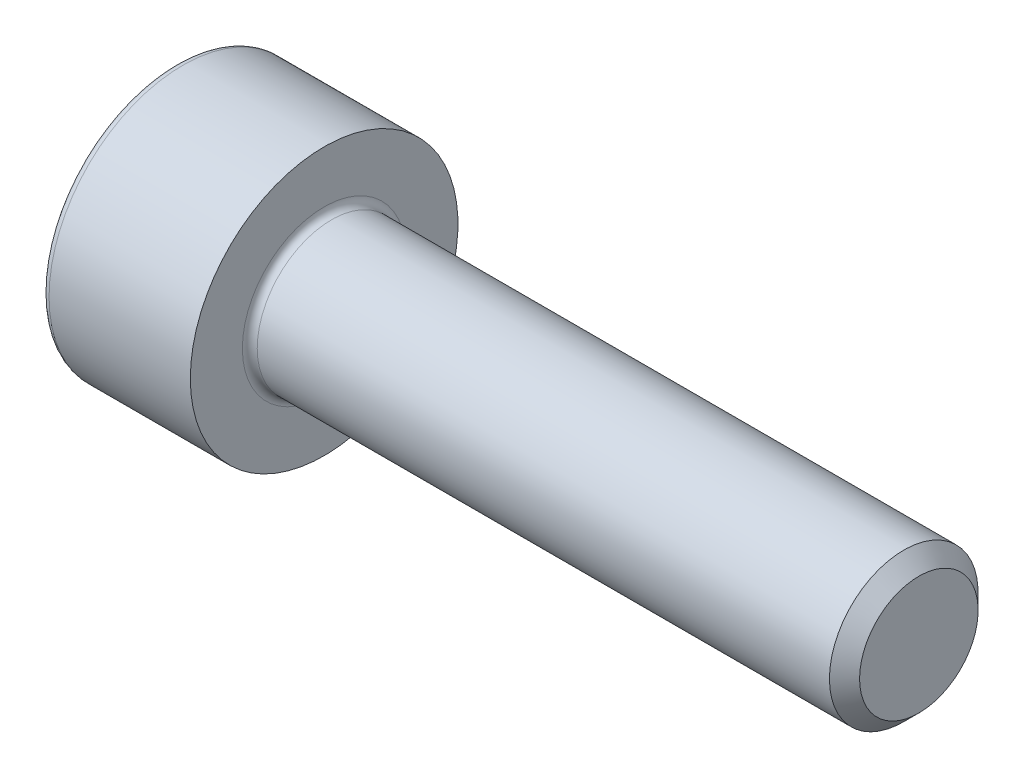
SolidWorks part; units mm, degrees
ref_plane "Front" through (0, 0, 0) normal (0, 0, 1) x (1, 0, 0)
ref_plane "Top" through (0, 0, 0) normal (0, 1, 0) x (1, 0, 0)
ref_plane "Right" through (0, 0, 0) normal (1, 0, 0) x (0, 0, -1)
sketch "Sketch1" plane through (0, 0, 0) normal (0, 0, 1) x (1, 0, 0)
  line L0 (9.7465, 1.25) -> (0.125, 1.25)
  line L1 (-2.5, 2.125) -> (-2.5, 0)
  line L2 (0, 2.25) -> (-2.375, 2.25)
  line L3 (0, 1.375) -> (0, 2.25)
  line L4 (10, 0.9965) -> (10, 0)
  line L5 (10, 0.9965) -> (9.7465, 1.25)
  line L6 (-2.5, 0) -> (0, 0) construction
  line L7 (-2.5, 0) -> (10, 0)
  arc A0 (-2.375, 2.25) -> (-2.5, 2.125) centre (-2.375, 2.125) ccw
  arc A1 (0, 1.375) -> (0.125, 1.25) centre (0.125, 1.375) ccw
  point P12 (0, 1.8125)
  dimension "D5" = 0.125
  dimension "D1" = 2.5
  dimension "D2" = 4.5
  dimension "D3" = 135
  dimension "D4" = 0.3585
  dimension "D6" = 10
  dimension "D7" = 2.5
revolve "Revolve1" add sketch "Sketch1" angle 360 about L7
sketch "Sketch2" plane through (-2.5, 0, 0) normal (-1, 0, 0) x (0, 0, 1)
  line L7 (1.025, 0.5918) -> (0, 1.1836)
  line L8 (0, 1.1836) -> (-1.025, 0.5918)
  line L9 (-1.025, 0.5918) -> (-1.025, -0.5918)
  line L10 (-1.025, -0.5918) -> (0, -1.1836)
  line L11 (0, -1.1836) -> (1.025, -0.5918)
  line L12 (1.025, -0.5918) -> (1.025, 0.5918)
  circle A0 centre (0, 0) radius 1.025 construction
  dimension "D1" = 2.05
extrude "Cut-Extrude1" cut sketch "Sketch2" against normal blind 1.1
